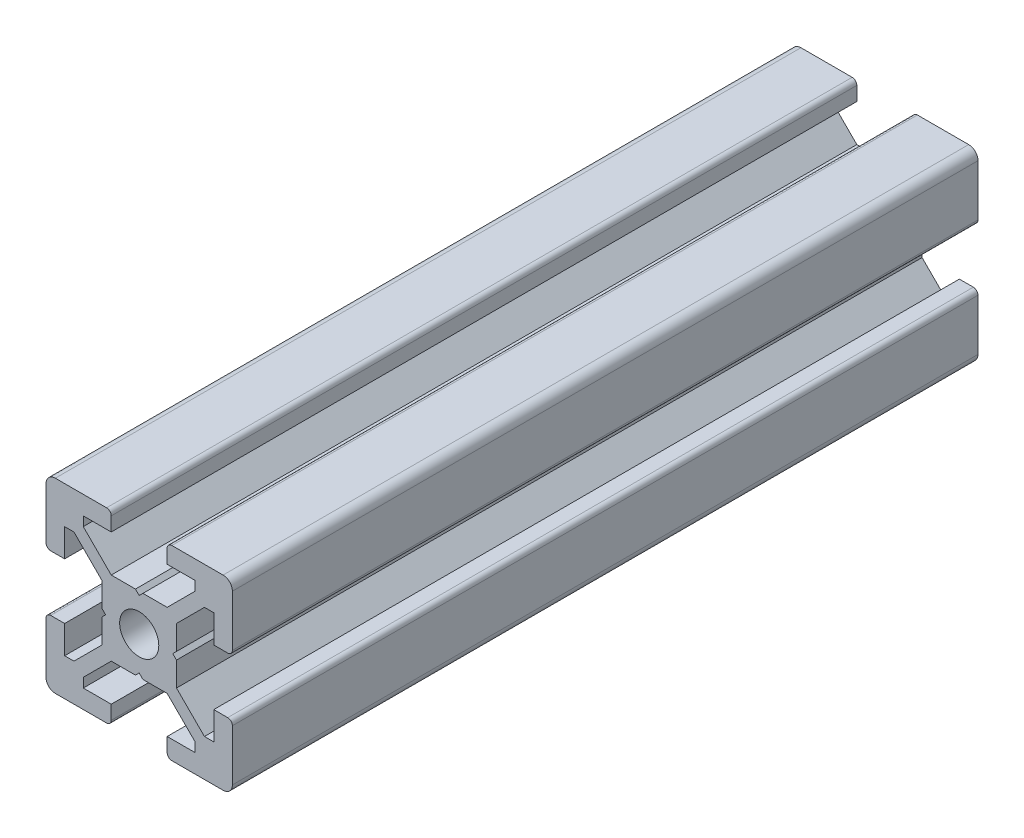
SolidWorks part; units mm, degrees
material "Lega 6061"
ref_plane "Piano frontale" through (0, 0, 0) normal (0, 0, 1) x (1, 0, 0)
ref_plane "Piano superiore" through (0, 0, 0) normal (0, 1, 0) x (1, 0, 0)
ref_plane "Piano destro" through (0, 0, 0) normal (1, 0, 0) x (0, 0, -1)
sketch "Schizzo1" plane through (0, 0, 0) normal (0, 0, 1) x (1, 0, 0)
  line L0 (0, 0) -> (-10, 0) construction
  line L1 (0, 0) -> (0, 10) construction
  line L2 (-3.6, 0) -> (-4, 0.4)
  line L3 (-4, 0.4) -> (-4, 3)
  line L4 (-4, 3) -> (-7, 6)
  line L5 (-7, 6) -> (-8, 6)
  line L6 (-8, 6) -> (-8, 3)
  line L7 (-8, 3) -> (-9.5, 3)
  line L8 (-10, 3.5) -> (-10, 9)
  line L9 (0, 0) -> (-10, 10) construction
  line L10 (0, 3.6) -> (-0.4, 4)
  line L11 (-0.4, 4) -> (-3, 4)
  line L12 (-3, 4) -> (-6, 7)
  line L13 (-6, 7) -> (-6, 8)
  line L14 (-6, 8) -> (-3, 8)
  line L15 (-3, 8) -> (-3, 9.5)
  line L16 (-3.5, 10) -> (-9, 10)
  line L17 (0, 0) -> (-10, -10) construction
  line L18 (-3.5, -10) -> (-9, -10)
  line L19 (-3, -8) -> (-3, -9.5)
  line L20 (-6, -8) -> (-3, -8)
  line L21 (-6, -7) -> (-6, -8)
  line L22 (-3, -4) -> (-6, -7)
  line L23 (-0.4, -4) -> (-3, -4)
  line L24 (0, -3.6) -> (-0.4, -4)
  line L25 (-10, -3.5) -> (-10, -9)
  line L26 (-8, -3) -> (-9.5, -3)
  line L27 (-8, -6) -> (-8, -3)
  line L28 (-7, -6) -> (-8, -6)
  line L29 (-4, -3) -> (-7, -6)
  line L30 (-4, -0.4) -> (-4, -3)
  line L31 (-3.6, 0) -> (-4, -0.4)
  line L32 (0, 0) -> (10, -10) construction
  line L33 (0, 0) -> (10, 10) construction
  line L34 (3.6, 0) -> (4, -0.4)
  line L35 (4, -0.4) -> (4, -3)
  line L36 (4, -3) -> (7, -6)
  line L37 (7, -6) -> (8, -6)
  line L38 (8, -6) -> (8, -3)
  line L39 (8, -3) -> (9.5, -3)
  line L40 (10, -3.5) -> (10, -9)
  line L41 (0, -3.6) -> (0.4, -4)
  line L42 (0.4, -4) -> (3, -4)
  line L43 (3, -4) -> (6, -7)
  line L44 (6, -7) -> (6, -8)
  line L45 (6, -8) -> (3, -8)
  line L46 (3, -8) -> (3, -9.5)
  line L47 (3.5, -10) -> (9, -10)
  line L48 (3.5, 10) -> (9, 10)
  line L49 (3, 8) -> (3, 9.5)
  line L50 (6, 8) -> (3, 8)
  line L51 (6, 7) -> (6, 8)
  line L52 (3, 4) -> (6, 7)
  line L53 (0.4, 4) -> (3, 4)
  line L54 (0, 3.6) -> (0.4, 4)
  line L55 (10, 3.5) -> (10, 9)
  line L56 (8, 3) -> (9.5, 3)
  line L57 (8, 6) -> (8, 3)
  line L58 (7, 6) -> (8, 6)
  line L59 (4, 3) -> (7, 6)
  line L60 (4, 0.4) -> (4, 3)
  line L61 (3.6, 0) -> (4, 0.4)
  arc A0 (-10, 9) -> (-9, 10) centre (-9, 9) cw
  arc A1 (-3, 9.5) -> (-3.5, 10) centre (-3.5, 9.5) ccw
  arc A2 (-9.5, 3) -> (-10, 3.5) centre (-9.5, 3.5) cw
  arc A3 (-9.5, -3) -> (-10, -3.5) centre (-9.5, -3.5) ccw
  arc A4 (-3, -9.5) -> (-3.5, -10) centre (-3.5, -9.5) cw
  arc A5 (-10, -9) -> (-9, -10) centre (-9, -9) ccw
  arc A6 (10, -9) -> (9, -10) centre (9, -9) cw
  arc A7 (3, -9.5) -> (3.5, -10) centre (3.5, -9.5) ccw
  arc A8 (9.5, -3) -> (10, -3.5) centre (9.5, -3.5) cw
  arc A9 (9.5, 3) -> (10, 3.5) centre (9.5, 3.5) ccw
  arc A10 (3, 9.5) -> (3.5, 10) centre (3.5, 9.5) cw
  arc A11 (10, 9) -> (9, 10) centre (9, 9) ccw
  circle A12 centre (0, 0) radius 2.1
  point P24 (-3, 10)
  point P27 (-10, 3)
  point P49 (-10, -3)
  point P50 (-3, -10)
  point P92 (3, -10)
  point P93 (10, -3)
  point P94 (10, 3)
  point P95 (3, 10)
  dimension "D2" = 1
  dimension "D12" = 0.5
  dimension "D13" = 4.2
  dimension "D3" = 8
  dimension "D4" = 0.4
  dimension "D5" = 45
  dimension "D6" = 6
  dimension "D7" = 12
  dimension "D8" = 20
  dimension "D9" = 2
  dimension "D10" = 4
  dimension "D11" = 45
extrude "Estrusione-Estrusione1" add sketch "Schizzo1" along normal blind 80
